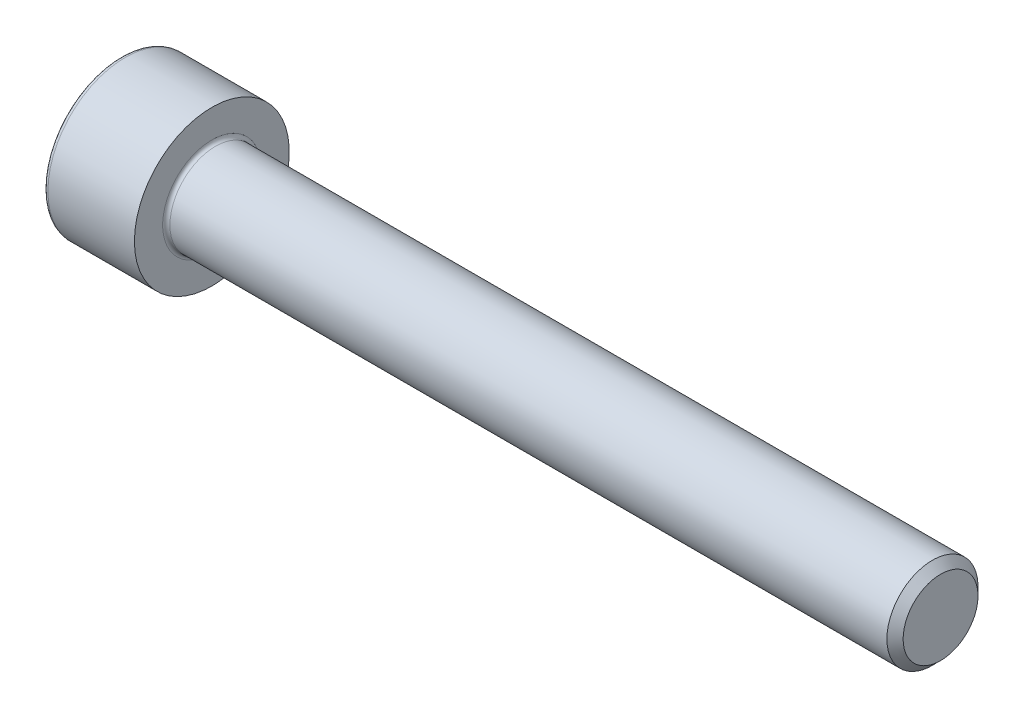
SolidWorks part; units mm, degrees
revolve "Base-Revolve" add sketch "BodySke"
sketch "BodySke" plane through (0, 0, 0) normal (0, 0, 1) x (1, 0, 0)
  line L0 (0, 0) -> (0, 4.25)
  line L1 (0, 4.25) -> (5, 4.25)
  line L2 (5, 4.25) -> (5, 2.5)
  line L3 (5, 2.5) -> (44.555, 2.5)
  line L4 (45, 2.055) -> (45, 0)
  line L5 (45, 0) -> (0, 0)
  line L6 (-31.75, 0) -> (127, 0) construction
  line L8 (45, 2.055) -> (44.555, 2.5)
  line L10 (45, -2.055) -> (44.555, -2.5) construction
  line L11 (5.8, 9.525) -> (5.8, 3.175) construction
  line L12 (23, 9.525) -> (23, 3.175) construction
  line L13 (-15, 9.525) -> (-15, 3.175) construction
  dimension "Head_ht" = 5
  dimension "Length" = 40
  dimension "Body_ch_ang" = 45
  dimension "Diameter" = 5
  dimension "Minor_dia" = 4.11
  dimension "Advance" = 0.8
  dimension "Thread_nom" = 22
  dimension "Thread_length" = 60
  dimension "Head_dia" = 8.5
cosmetic thread "ThreadCosmetic"
fillet "Fillet1" radius 0.2 1 edges at (5, 0, 2.5)
fillet "Fillet2" radius 0.25 1 edges at (0, 0, 4.25)
ref_plane "Plane1" through (0, 0, 0) normal (0, 0, 1) x (1, 0, 0)
ref_plane "Plane2" through (0, 0, 0) normal (0, 1, 0) x (1, 0, 0)
ref_plane "Plane3" through (0, 0, 0) normal (1, 0, 0) x (0, 0, -1)
sketch "Sketch2" plane through (0, 0, 0) normal (0, 0, 1) x (1, 0, 0)
  line L0 (0, 2.042) -> (2.5, 2.042)
  line L1 (2.5, 2.042) -> (3.6789, 0)
  line L2 (-31.75, 0) -> (127, 0) construction
  line L3 (3.6789, 0) -> (0, 0)
  line L4 (0, 0) -> (0, 2.042)
  line L6 (0, 0) -> (47.625, 0) construction
  dimension "D1" = 2.042
  dimension "D2" = 60
  dimension "Depth" = 2.5
revolve "Hex-PreBroach" cut sketch "Sketch2" angle 360 about L6
sketch "Sketch3" plane through (0, 0, 0) normal (-1, 0, 0) x (0, 0.5, 0.866)
  line L0 (1.1789, 2.042) -> (-1.1789, 2.042)
  line L1 (-1.1789, 2.042) -> (-2.3579, 0)
  line L2 (1.1789, 2.042) -> (2.3579, 0)
  line L3 (1.1789, -2.042) -> (2.3579, 0)
  line L4 (1.1789, -2.042) -> (-1.1789, -2.042)
  line L5 (-1.1789, -2.042) -> (-2.3579, 0)
  dimension "D1" = 2.042
  dimension "D2" = 2.042
  dimension "Hex_size" = 4.084
extrude "Hex" cut sketch "Sketch3" against normal blind 2.5
sketch "ThdSchSke" plane through (0, 0, 0) normal (0, 0, 1) x (1, 0, 0)
  line L0 (23, -2.055) -> (22.6884, -2.5)
  line L1 (23, -2.055) -> (23.3116, -2.5)
  line L2 (23.3116, -2.5) -> (23.3116, -3.125)
  line L3 (-3.175, 0) -> (5.1513, 0) construction
  line L4 (0, 4) -> (0, -4) construction
  line L5 (23.3116, -3.125) -> (22.6884, -3.125)
  line L6 (22.6884, -3.125) -> (22.6884, -2.5)
  dimension "Thread_minor" = 4.11
  dimension "Diameter" = 5
  dimension "Start" = 23
revolve "ThreadSchematic" [suppressed] cut sketch "ThdSchSke" angle 360 about L3
pattern_linear "ThdSchPat" [suppressed]
scale "Scale1" scale about origin uniform scaling yes scale factor 0.630435
equation "\"D2@Sketch3\" = \"Hex_size@Sketch3\" / 2"
equation "\"D1@Sketch3\" = \"Hex_size@Sketch3\" / 2"
equation "\"D1@Sketch2\" = \"Hex_size@Sketch3\" / 2"
equation "\"Thread_minor@ThreadCosmetic\"  =  \"Minor_dia@BodySke\""
equation "\"Depth@Sketch2\" =  \"Key_eng@Hex\""
equation "\"Thread_length@ThreadCosmetic\" = ((sgn( (\"Length@BodySke\" - \"Advance@BodySke\" * 3.0) - \"Thread_nom@BodySke\" )-1)*( (\"Length@BodySke\" - \"Advance@BodySke\" * 3.0) - \"Thread_nom@BodySke\" ))/-2+ \"Thread_nom@BodySke\""
equation "\"Thread_minor@ThdSchSke\" = \"Minor_dia@BodySke\""
equation "\"Diameter@ThdSchSke\" = \"Diameter@BodySke\""
equation "\"Overcut@ThdSchSke\" = \"Diameter@BodySke\" * 1.25"
equation "\"Start@ThdSchSke\" = \"Head_ht@BodySke\" + \"Length@BodySke\" - \"Thread_length@ThreadCosmetic\"  '---Non-countersunk---"
equation "\"Num_threads@ThdSchPat\" = int( \"Thread_length@ThreadCosmetic\" / \"Advance@BodySke\" + 0.999 )  + 1"
equation "\"Advance@ThdSchPat\" = \"Thread_length@ThreadCosmetic\" /  (\"Num_threads@ThdSchPat\" - 1) 'relax it"
equation "\"Num_threads@ThdSchPat\" = \"Num_threads@ThdSchPat\" - sgn( \"Num_threads@ThdSchPat\" - 1) '---chamfered tips only---"
